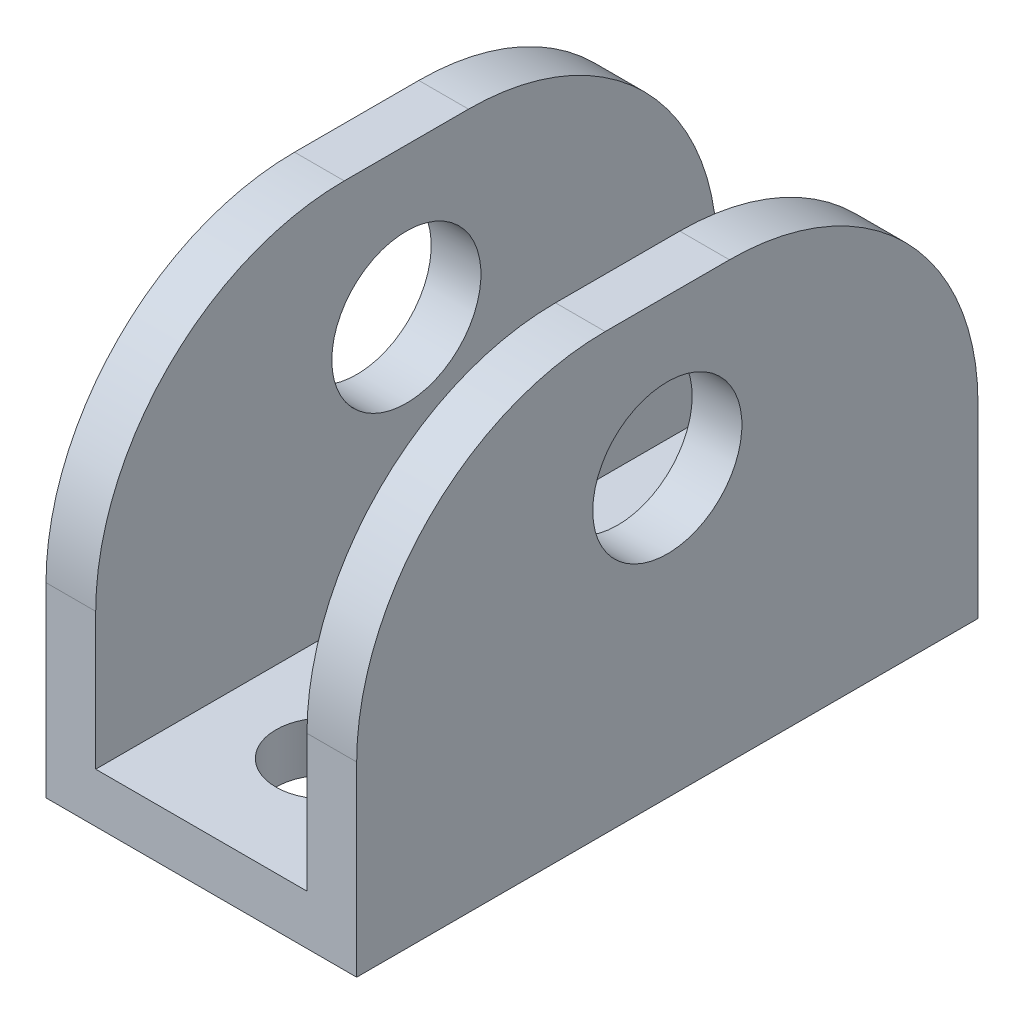
SolidWorks part; units mm, degrees
material "6061-T6 (SS)"
ref_plane "Front Plane" through (0, 0, 0) normal (0, 0, 1) x (1, 0, 0)
ref_plane "Top Plane" through (0, 0, 0) normal (0, 1, 0) x (1, 0, 0)
ref_plane "Right Plane" through (0, 0, 0) normal (1, 0, 0) x (0, 0, -1)
sketch "Sketch1" plane through (0, 0, 0) normal (1, 0, 0) x (0, 0, -1)
  line L1 (-25, 17.5) -> (25, 17.5)
  line L2 (-25, 17.5) -> (-25, -17.5)
  line L3 (-25, -17.5) -> (25, -17.5)
  line L4 (25, 17.5) -> (25, -17.5)
  line L5 (-25, 17.5) -> (25, -17.5) construction
  line L6 (-25, -17.5) -> (25, 17.5) construction
  point P0 (0, 0)
  dimension "D1" = 50
  dimension "D2" = 35
extrude "Boss-Extrude1" add sketch "Sketch1" along normal blind 25
sketch "Sketch2" plane through (0, 17.5, 0) normal (0, 1, 0) x (1, 0, 0)
  line L0 (25, 25) -> (0, 25) construction
  line L1 (4, 25) -> (21, 25)
  line L2 (4, 25) -> (4, -25)
  line L3 (4, -25) -> (21, -25)
  line L4 (21, 25) -> (21, -25)
  line L5 (25, -25) -> (0, -25) construction
  line L6 (25, 25) -> (25, -25) construction
  line L7 (0, 25) -> (0, -25) construction
  dimension "D1" = 4
  dimension "D2" = 4
extrude "Cut-Extrude1" cut sketch "Sketch2" against normal offset from surface (31 mm away) 4 up to face at (12.5, -17.5, 0)
sketch "Sketch4" plane through (0, 0, 0) normal (-1, 0, 0) x (0, 0, 1)
  line L0 (25, -17.5) -> (-25, -17.5) construction
  circle A0 centre (0, 5.5) radius 6
  dimension "D2" = 12
  dimension "D1" = 23
extrude "Cut-Extrude2" cut sketch "Sketch4" against normal through all
sketch "Sketch5" plane through (0, -17.5, 0) normal (0, -1, 0) x (1, 0, 0)
  line L1 (0, 25) -> (0, -25) construction
  line L2 (25, 25) -> (0, 25) construction
  circle A0 centre (12.5, 15) radius 4
  circle A1 centre (12.5, -15) radius 4
  dimension "D1" = 8
  dimension "D2" = 12.5
  dimension "D3" = 30
  dimension "D4" = 10
extrude "Cut-Extrude3" cut sketch "Sketch5" against normal up to surface (4 mm away) up to face at (12.5, -13.5, 0)
fillet "Fillet1" radius 20 4 edges at (23, 17.5, -25) (23, 17.5, 25) (2, 17.5, 25) (2, 17.5, -25)
sketch "Sketch6" plane through (0, 0, 0) normal (-1, 0, 0) x (0, 0, 1)
  line L1 (-29.3063, 22.6173) -> (30.6937, 22.6173)
  line L2 (-29.3063, 22.6173) -> (-29.3063, -17.3827)
  line L3 (-29.3063, -17.3827) -> (30.6937, -17.3827)
  line L4 (30.6937, 22.6173) -> (30.6937, -17.3827)
  dimension "D1" = 60
  dimension "D2" = 40
